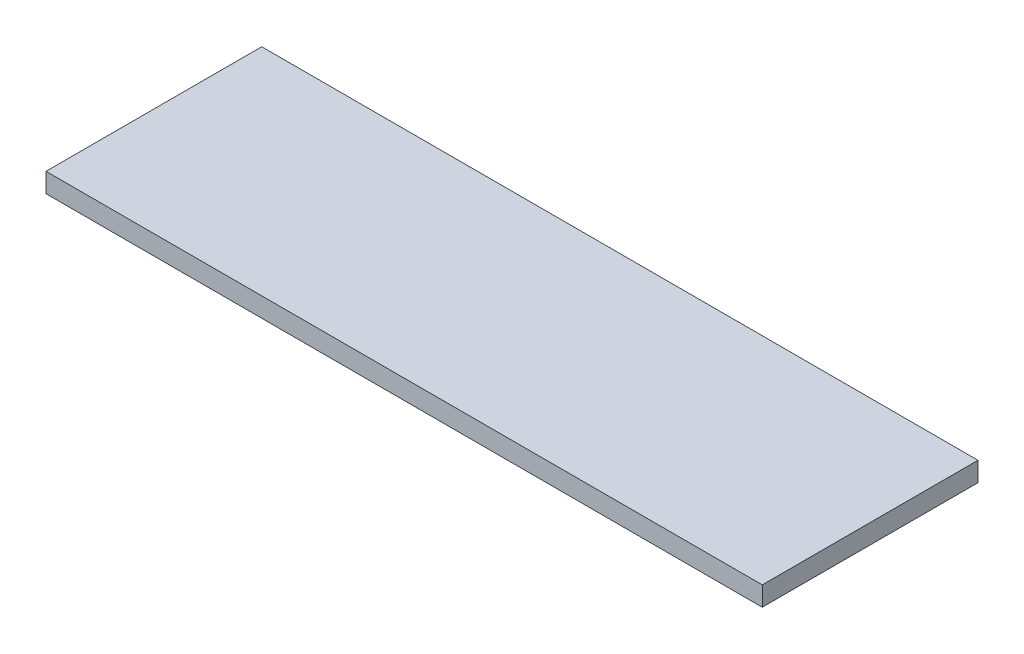
SolidWorks part; units mm, degrees
ref_plane "前视基准面" through (0, 0, 0) normal (0, 0, 1) x (1, 0, 0)
ref_plane "上视基准面" through (0, 0, 0) normal (0, 1, 0) x (1, 0, 0)
ref_plane "右视基准面" through (0, 0, 0) normal (1, 0, 0) x (0, 0, -1)
sketch "草图1" plane through (0, 0, 0) normal (0, 1, 0) x (1, 0, 0)
  line L1 (0, 0) -> (66.4, 0)
  line L2 (0, 0) -> (0, 20)
  line L3 (0, 20) -> (66.4, 20)
  line L4 (66.4, 0) -> (66.4, 20)
  dimension "D1" = 66.4
  dimension "D2" = 20
extrude "凸台-拉伸1" add sketch "草图1" along normal blind 1.8
